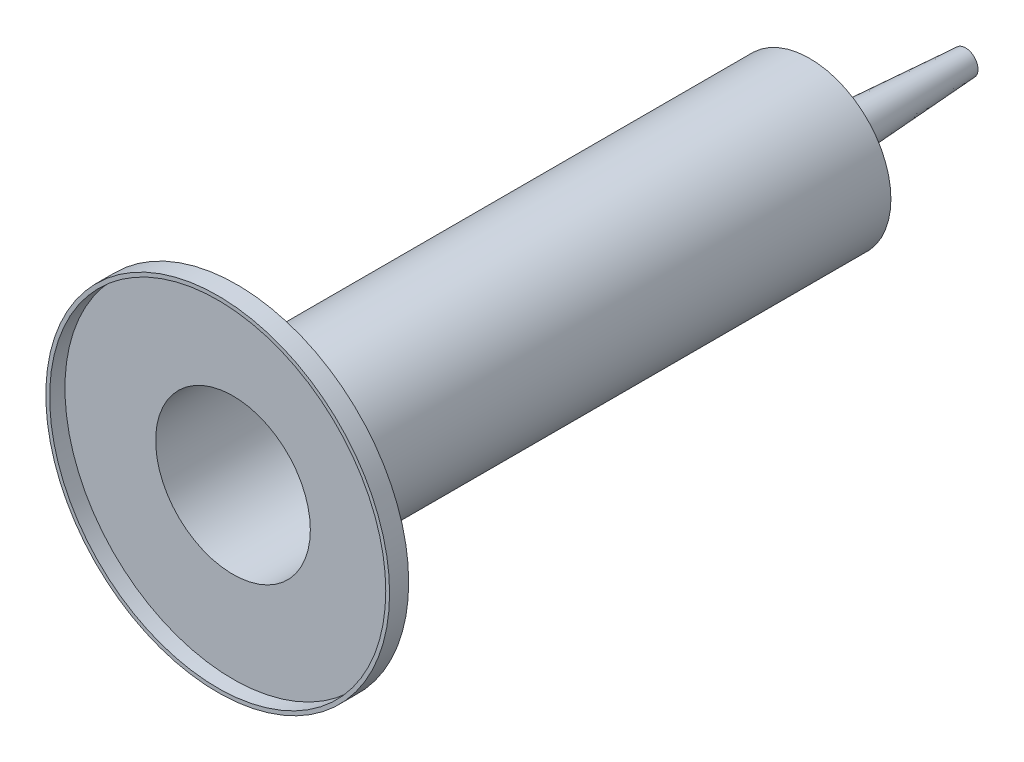
SolidWorks part; units mm, degrees
ref_plane "Front Plane" through (0, 0, 0) normal (0, 0, 1) x (1, 0, 0)
ref_plane "Top Plane" through (0, 0, 0) normal (0, 1, 0) x (1, 0, 0)
ref_plane "Right Plane" through (0, 0, 0) normal (1, 0, 0) x (0, 0, -1)
sketch "Sketch1" plane through (0, 0, 0) normal (0, 0, 1) x (1, 0, 0)
  circle A0 centre (0, 0) radius 21.25
  dimension "D1" = 42.5
extrude "Boss-Extrude1" add sketch "Sketch1" along normal blind 150
sketch "Sketch2" plane through (0, 0, 150) normal (0, 0, 1) x (1, 0, 0)
  circle A0 centre (0, 0) radius 45
  dimension "D1" = 90
extrude "Boss-Extrude2" add sketch "Sketch2" along normal blind 5
sketch "Sketch4" plane through (0, 0, 0) normal (1, 0, 0) x (0, 0, -1)
  line L0 (0, 21.25) -> (6.8, 5.35)
  line L1 (6.8, 5.35) -> (40.8, 3.25)
  line L2 (40.8, 3.25) -> (40.8, 0)
  line L3 (0, 0) -> (40.8, 0) construction
  line L4 (40.8, 0) -> (0, 0)
  line L5 (0, 0) -> (0, 21.25)
  dimension "D1" = 6.5
  dimension "D2" = 10.7
  dimension "D3" = 34
  dimension "D4" = 6.8
revolve "Revolve1" add sketch "Sketch4" angle 360 about L3
shell "Shell1" thickness 1
